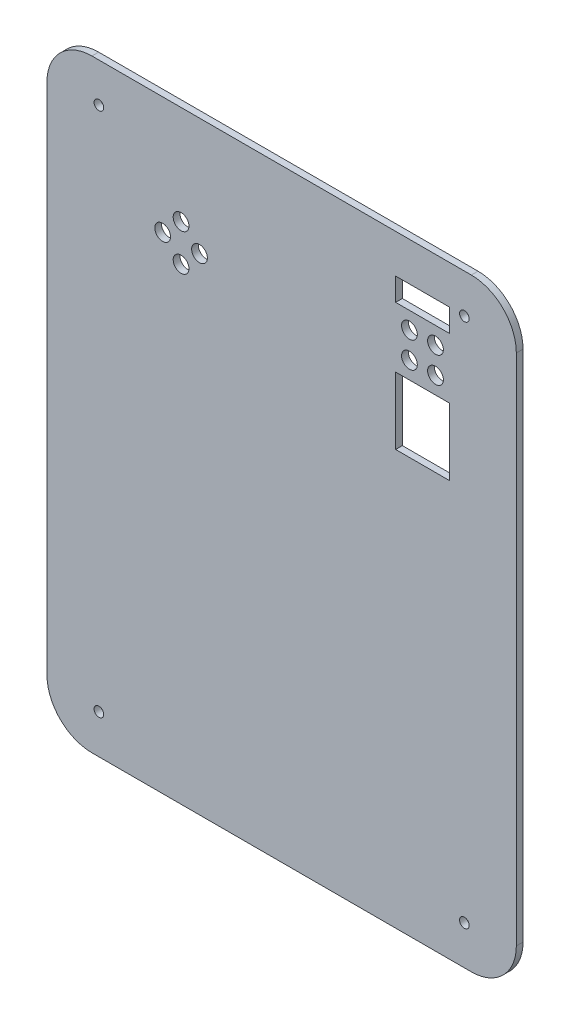
SolidWorks part; units mm, degrees
ref_plane "Front Plane" through (0, 0, 0) normal (1, 0, 0) x (0, 1, 0)
ref_plane "Top Plane" through (0, 0, 0) normal (0, 0, 1) x (0, 1, 0)
ref_plane "Right Plane" through (0, 0, 0) normal (0, 1, 0) x (-1, 0, 0)
sketch "Sketch1" plane through (0, 0, 0) normal (0, 0, 1) x (0, 1, 0)
  line L5 (-97.2566, -88.9) -> (97.2566, -88.9)
  line L6 (-114.3, -71.8566) -> (-114.3, 71.8566)
  line L7 (-97.2566, 88.9) -> (97.2566, 88.9)
  line L8 (114.3, -71.8566) -> (114.3, 71.8566)
  arc A0 (-114.3, 71.8566) -> (-97.2566, 88.9) centre (-97.2566, 71.8566) cw
  arc A1 (-97.2566, -88.9) -> (-114.3, -71.8566) centre (-97.2566, -71.8566) cw
  arc A2 (97.2566, -88.9) -> (114.3, -71.8566) centre (97.2566, -71.8566) ccw
  arc A3 (97.2566, 88.9) -> (114.3, 71.8566) centre (97.2566, 71.8566) cw
  point P15 (114.3, 0)
  point P20 (0, 88.9)
  dimension "D1" = 17.0434
  dimension "D2" = 177.8
  dimension "D3" = 228.6
extrude "Boss-Extrude1" add sketch "Sketch1" along normal blind 2.54
sketch "Sketch2" plane through (0, 0, 2.54) normal (0, 0, 1) x (1, 0, 0)
  line L0 (0, 223.1681) -> (0, -217.0396) construction
  line L1 (-162.9401, 0) -> (143.5585, 0) construction
  point P11 (69.2191, -99.5086)
  point P12 (-69.2191, 99.5086)
  point P13 (-69.2191, -99.5086)
  point P14 (69.2191, 99.5086)
  dimension "D10" = 99.5086
  dimension "D3" = 69.2191
  dimension "D4" = 69.2191
  dimension "D5" = 99.5086
  dimension "D2" = 99.5086
  dimension "D6" = 69.2191
  dimension "D7" = 99.5086
  dimension "D8" = 69.2191
sketch "Sketch6" plane through (0, 0, 2.54) normal (0, 0, 1) x (1, 0, 0)
  line L0 (53.34, 139.097) -> (53.34, 21.4757) construction
  line L2 (43.18, 68.1355) -> (63.5, 68.1355)
  line L3 (-38.1, 127.2984) -> (-38.1, 26.2104) construction
  line L5 (63.5, 68.1355) -> (63.5, 42.7355)
  line L20 (-38.1, 69.85) -> (-66.04, 69.85) construction
  line L21 (-38.1, 69.85) -> (-38.1, 97.79) construction
  line L22 (-104.6586, 69.85) -> (20.7446, 69.85) construction
  line L24 (63.5, 42.7355) -> (43.18, 42.7355)
  line L25 (117.4238, 79.5655) -> (-13.9103, 79.5655) construction
  line L27 (58.2791, 84.5046) -> (58.2791, 79.5655) construction
  line L28 (58.2791, 84.5046) -> (53.34, 84.5046) construction
  line L30 (58.2791, 79.5655) -> (58.2791, 74.6264) construction
  line L31 (58.2791, 84.5046) -> (53.34, 79.5655) construction
  line L32 (53.34, 79.5655) -> (58.2791, 74.6264) construction
  line L33 (53.34, 79.5655) -> (48.4009, 74.6264) construction
  line L34 (53.34, 79.5655) -> (48.4009, 84.5046) construction
  line L35 (58.2791, 74.6264) -> (53.34, 74.6264) construction
  line L36 (53.34, 74.6264) -> (48.4009, 74.6264) construction
  line L37 (48.4009, 74.6264) -> (48.4009, 79.5655) construction
  line L38 (48.4009, 79.5655) -> (48.4009, 84.5046) construction
  line L39 (48.4009, 84.5046) -> (53.34, 84.5046) construction
  line L40 (43.18, 90.9955) -> (63.5, 90.9955)
  line L41 (63.5, 90.9955) -> (63.5, 99.6315)
  line L42 (63.5, 99.6315) -> (43.18, 99.6315)
  line L43 (43.18, 99.6315) -> (43.18, 90.9955)
  line L44 (43.18, 42.7355) -> (43.18, 68.1355)
  line L45 (-162.9401, 0) -> (143.5585, 0) construction
  line L47 (0, 223.1681) -> (0, -217.0396) construction
  circle A6 centre (58.2791, 84.5046) radius 2.9845
  circle A7 centre (58.2791, 74.6264) radius 2.9845
  circle A8 centre (48.4009, 74.6264) radius 2.9845
  circle A9 centre (48.4009, 84.5046) radius 2.9845
  circle A10 centre (-38.1, 76.835) radius 2.9845
  circle A11 centre (-31.115, 69.85) radius 2.9845
  circle A12 centre (-38.1, 62.865) radius 2.9845
  circle A13 centre (-45.085, 69.85) radius 2.9845
  dimension "D7" = 5.969
  dimension "D8" = 5.969
  dimension "D9" = 5.969
  dimension "D10" = 5.969
  dimension "D11" = 5.969
  dimension "D12" = 5.969
  dimension "D13" = 5.969
  dimension "D14" = 5.969
  dimension "D4" = 6.985
  dimension "D6" = 6.985
  dimension "D15" = 6.985
  dimension "D16" = 6.985
  dimension "D17" = 6.985
  dimension "D18" = 6.985
  dimension "D19" = 8.636
  dimension "D20" = 11.43
  dimension "D21" = 20.32
  dimension "D22" = 10.16
  dimension "D23" = 10.16
  dimension "D24" = 20.32
  dimension "D25" = 25.4
  dimension "D26" = 11.43
  dimension "D27" = 69.85
  dimension "D28" = 38.1
  dimension "D3" = 53.34
  dimension "D5" = 79.5655
extrude "Cut-Extrude1" cut sketch "Sketch6" against normal through all
hole_wizard "#27 (0.144) Diameter Hole1" positions "Sketch2" profile "Sketch7" hole size "#27" standard "ANSI Inch" end condition through all
sketch "Sketch7" plane through (69.2191, 99.5086, 2.54) normal (1, 0, 0) x (0, -1, 0)
  line L0 (0, 0) -> (0, 2.54)
  line L1 (0, 2.54) -> (1.8288, 2.54)
  line L2 (1.8288, 2.54) -> (1.8288, 0)
  line L5 (1.8288, 0) -> (0, 0)
  line L11 (0, -6.35) -> (0, 107.95) construction
  dimension "Thru Hole Dia." = 3.6576
  dimension "Thru Hole Depth" = 2.54
equation "\"D16@Sketch6\"=\"D15@Sketch6\""
equation "\"D17@Sketch6\"=\"D15@Sketch6\""
equation "\"D18@Sketch6\"=\"D15@Sketch6\""
equation "\"D4@Sketch2\"=\"D3@Sketch2\""
equation "\"D5@Sketch2\"=\"D10@Sketch2\""
equation "\"D2@Sketch2\"=\"D10@Sketch2\""
equation "\"D6@Sketch2\"=\"D3@Sketch2\""
equation "\"D7@Sketch2\"=\"D10@Sketch2\""
equation "\"D8@Sketch2\"=\"D3@Sketch2\""
